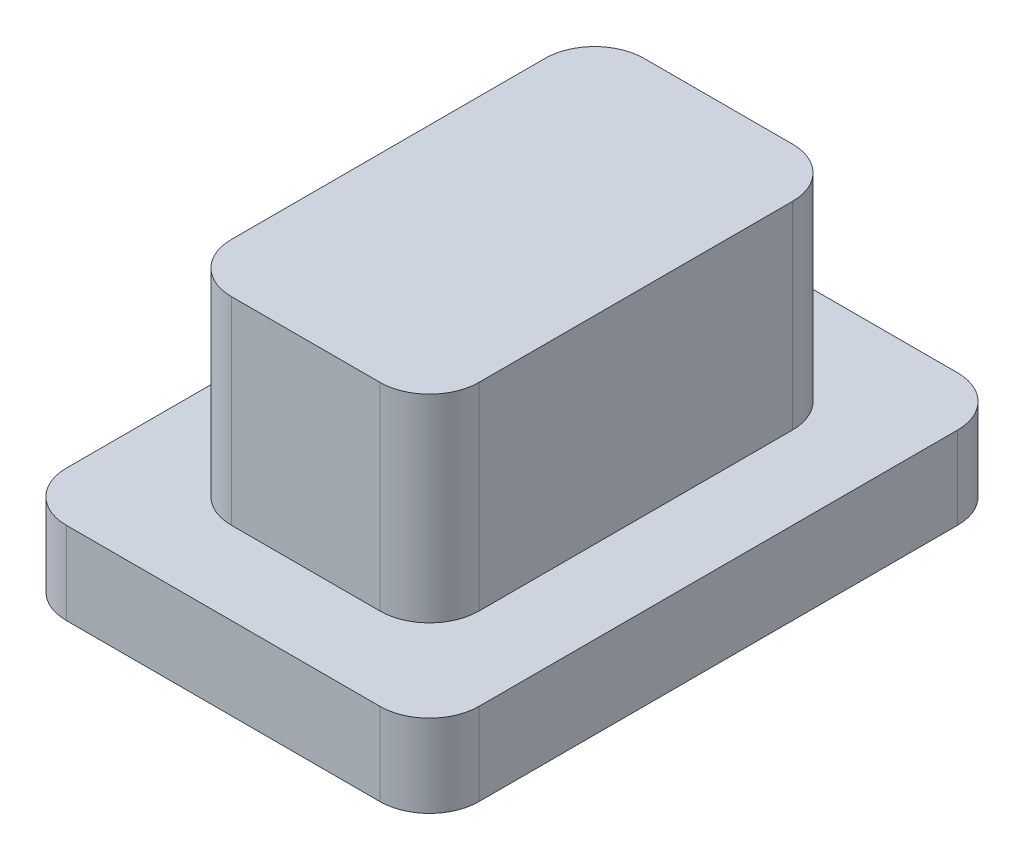
SolidWorks part; units mm, degrees
ref_plane "前视基准面" through (0, 0, 0) normal (0, 0, 1) x (1, 0, 0)
ref_plane "上视基准面" through (0, 0, 0) normal (0, 1, 0) x (1, 0, 0)
ref_plane "右视基准面" through (0, 0, 0) normal (1, 0, 0) x (0, 0, -1)
sketch "草图1" plane through (0, 0, 0) normal (0, 1, 0) x (1, 0, 0)
  line L1 (-2.5, 3.5) -> (2.5, 3.5)
  line L2 (-2.5, 3.5) -> (-2.5, -3.5)
  line L3 (-2.5, -3.5) -> (2.5, -3.5)
  line L4 (2.5, 3.5) -> (2.5, -3.5)
  line L5 (-2.5, 3.5) -> (2.5, -3.5) construction
  line L6 (-2.5, -3.5) -> (2.5, 3.5) construction
  point P0 (0, 0)
  dimension "D1" = 5
  dimension "D2" = 7
extrude "凸台-拉伸1" add sketch "草图1" along normal blind 1
sketch "草图2" plane through (0, 1, 0) normal (0, 1, 0) x (1, 0, 0)
  line L1 (-1.5, 2.5) -> (1.5, 2.5)
  line L2 (-1.5, 2.5) -> (-1.5, -2.5)
  line L3 (-1.5, -2.5) -> (1.5, -2.5)
  line L4 (1.5, 2.5) -> (1.5, -2.5)
  line L5 (-1.5, 2.5) -> (1.5, -2.5) construction
  line L6 (-1.5, -2.5) -> (1.5, 2.5) construction
  point P0 (0, 0)
  dimension "D1" = 3
  dimension "D2" = 5
extrude "凸台-拉伸2" add sketch "草图2" along normal blind 2.4
fillet "圆角1" radius 0.6 8 edges at (-1.5, 2.2, -2.5) (1.5, 2.2, -2.5) (1.5, 2.2, 2.5) (-1.5, 2.2, 2.5) (2.5, 0.5, -3.5) (-2.5, 0.5, -3.5) (2.5, 0.5, 3.5) (-2.5, 0.5, 3.5)
